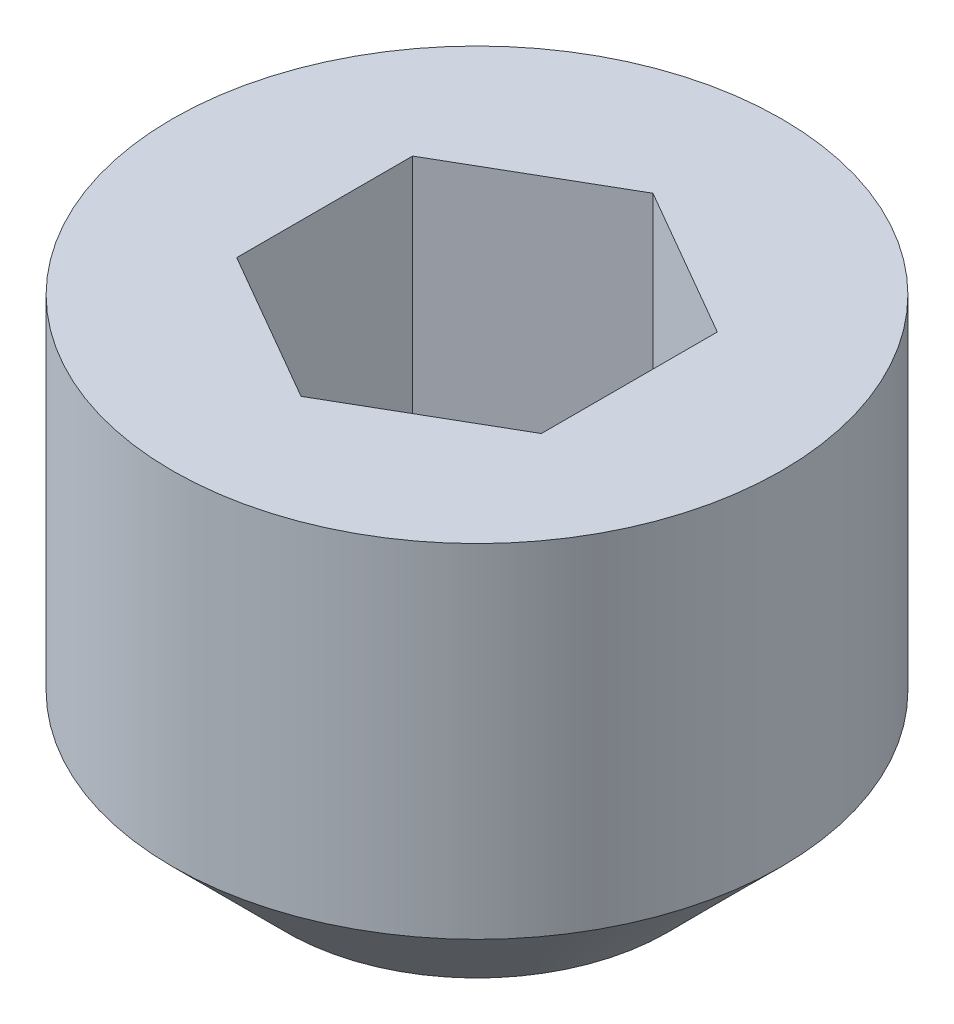
SolidWorks part; units mm, degrees
ref_plane "Front Plane" through (0, 0, 0) normal (0, 0, 1) x (1, 0, 0)
ref_plane "Top Plane" through (0, 0, 0) normal (0, 1, 0) x (1, 0, 0)
ref_plane "Right Plane" through (0, 0, 0) normal (1, 0, 0) x (0, 0, -1)
sketch "Sketch1" plane through (0, 0, 0) normal (0, 0, 1) x (1, 0, 0)
  line L0 (0, 3) -> (0, 0) construction
  line L2 (0, 3) -> (2, 3)
  line L3 (0, 3) -> (0, 0)
  line L4 (0, 0) -> (2, 0)
  line L5 (2, 3) -> (2, 0)
  dimension "SS_M" = 4
  dimension "SS_L" = 3
revolve "Revolve1" add sketch "Sketch1" angle 360 about L0
cosmetic thread "Cosmetic Thread1" parameters "SS_D1_s"=3.22
sketch "Sketch2" plane through (0, 0, 0) normal (0, 0, 1) x (1, 0, 0)
  line L0 (0, 3) -> (0, 0.9226) construction
  line L1 (0, 3) -> (1, 3)
  line L3 (1, 3) -> (1, 1.5)
  line L4 (1, 1.5) -> (0, 0.9226)
  line L5 (0, 0.9226) -> (0, 3)
  line L6 (2, 3) -> (-2, 3) construction
  dimension "D1" = 60
  dimension "SS_B" = 2
revolve "Cut-Revolve1" cut sketch "Sketch2" angle 360 about L0
sketch "Sketch3" plane through (0, 3, 0) normal (0, 1, 0) x (1, 0, 0)
  line L1 (0, 1.1547) -> (-1, 0.5774)
  line L2 (-1, 0.5774) -> (-1, -0.5774)
  line L3 (-1, -0.5774) -> (0, -1.1547)
  line L4 (0, -1.1547) -> (1, -0.5774)
  line L5 (1, -0.5774) -> (1, 0.5774)
  line L6 (1, 0.5774) -> (0, 1.1547)
  circle A0 centre (0, 0) radius 1 construction
  circle A1 centre (0, 0) radius 1 construction
extrude "Cut-Extrude1" cut sketch "Sketch3" against normal blind 1.5
sketch "Sketch4" plane through (0, 0, 0) normal (0, 0, 1) x (1, 0, 0)
  line L0 (0, 3) -> (0, 0) construction
  line L1 (2, 3) -> (2, 0) construction
  line L2 (-2, 0) -> (2, 0) construction
  line L3 (2, 0.75) -> (2, 0)
  line L4 (2, 0) -> (1.25, 0)
  line L5 (1.25, 0) -> (2, 0.75)
  dimension "D1" = 45
  dimension "SS_D_s" = 2.5
revolve "Cut-Revolve2" cut sketch "Sketch4" angle 360 about L0
